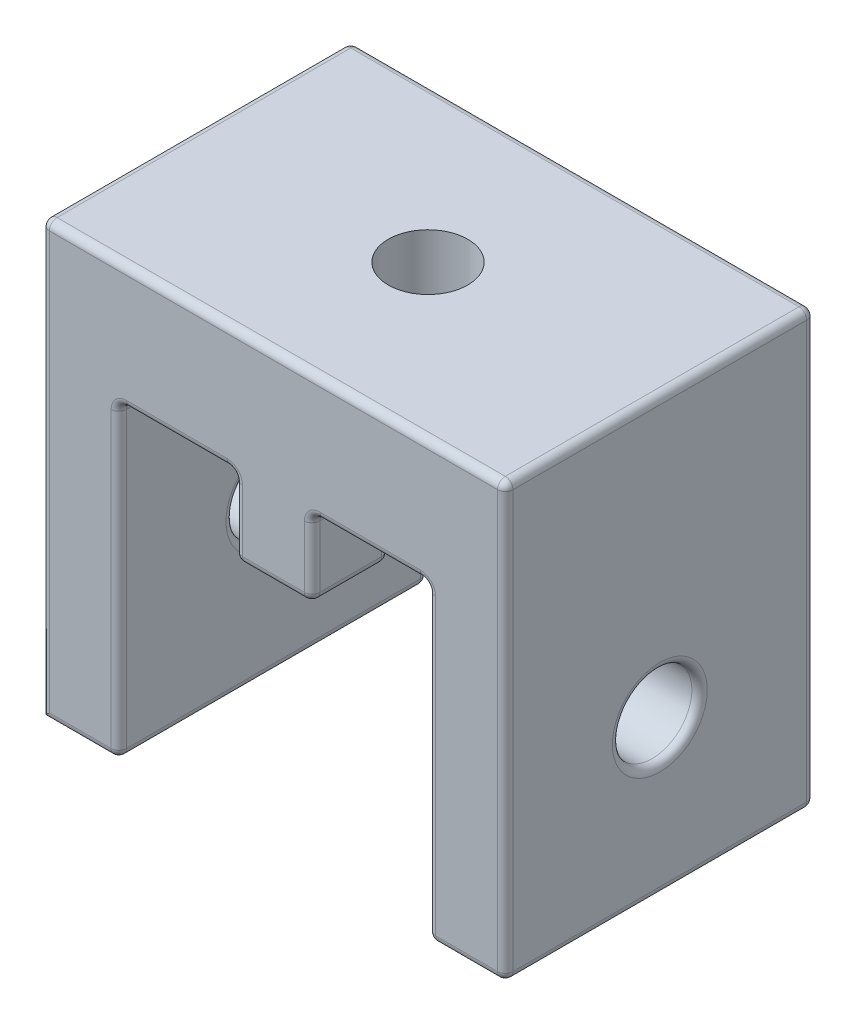
SolidWorks part; units mm, degrees
ref_plane "Front Plane" through (0, 0, 0) normal (0, 0, 1) x (1, 0, 0)
ref_plane "Top Plane" through (0, 0, 0) normal (0, 1, 0) x (1, 0, 0)
ref_plane "Right Plane" through (0, 0, 0) normal (1, 0, 0) x (0, 0, -1)
sketch "Sketch1" plane through (0, 0, 0) normal (0, 0, 1) x (1, 0, 0)
  line L0 (0, 0) -> (6.35, 0) construction
  line L1 (0, 0) -> (6.35, 0)
  line L2 (0, 0) -> (0, 35.56)
  line L3 (0, 35.56) -> (38.1, 35.56)
  line L4 (38.1, 0) -> (38.1, 35.56)
  line L5 (6.35, 0) -> (6.35, 25.4) construction
  line L6 (6.35, 25.4) -> (31.75, 25.4) construction
  line L7 (31.75, 25.4) -> (31.75, 0) construction
  line L8 (31.75, 0) -> (38.1, 0) construction
  line L9 (6.35, 0) -> (6.35, 25.4)
  line L10 (6.35, 25.4) -> (31.75, 25.4)
  line L11 (31.75, 25.4) -> (31.75, 0)
  line L12 (31.75, 0) -> (38.1, 0)
  dimension "D1" = 6.35
  dimension "D2" = 6.35
  dimension "D3" = 25.4
  dimension "D4" = 38.1
  dimension "D5" = 35.56
  dimension "D6" = 25.4
extrude "Boss-Extrude1" add sketch "Sketch1" along normal blind 25.4
sketch "Sketch2" plane through (0, 25.4, 0) normal (0, -1, 0) x (1, 0, 0)
  line L0 (0, 0) -> (19.05, 0) construction
  line L1 (6.35, 0) -> (31.75, 0) construction
  line L2 (19.05, 0) -> (19.05, 3.175) construction
  line L4 (22.225, 6.35) -> (15.875, 6.35)
  line L5 (22.225, 6.35) -> (22.225, 0)
  line L6 (22.225, 0) -> (15.875, 0)
  line L7 (15.875, 6.35) -> (15.875, 0)
  line L8 (22.225, 6.35) -> (15.875, 0) construction
  line L9 (22.225, 0) -> (15.875, 6.35) construction
  dimension "D1" = 6.35
  dimension "D2" = 6.35
extrude "Boss-Extrude2" add sketch "Sketch2" along normal blind 6.35
ref_plane "Plane1" through (0, 0, 12.7) normal (0, 0, 1) x (1, 0, 0)
mirror "Mirror1" about plane through (0, 0, 12.7) normal (0, 0, 1) of "Boss-Extrude2"
hole_wizard "#97 (0.0059) Diameter Hole3" positions "Sketch4" profile "Sketch3" hole size "#97" standard "Ansi Inch" end condition through all
sketch "Sketch4" plane through (0, 35.56, 0) normal (0, 1, 0) x (-1, 0, 0)
  line L0 (-38.1, 0) -> (0, 0) construction
  line L1 (0, 25.4) -> (0, 0) construction
  point P0 (-19.05, 12.7)
  point P2 (-19.05, 0)
  dimension "D1" = 12.7
  dimension "D2" = 19.05
sketch "Sketch3" plane through (19.05, 35.56, 12.7) normal (1, 0, 0) x (0, 0, 1)
  line L0 (0, 0) -> (0, 35.56)
  line L1 (0, 35.56) -> (3.2639, 35.56)
  line L2 (3.2639, 35.56) -> (3.2639, 0)
  line L5 (3.2639, 0) -> (0, 0)
  line L11 (0, -6.35) -> (0, 107.95) construction
  dimension "Thru Hole Dia." = 6.5278
  dimension "Thru Hole Depth" = 35.56
hole_wizard "#97 (0.0059) Diameter Hole1" positions "Sketch6" profile "Sketch5" hole size "#97" standard "Ansi Inch"
sketch "Sketch6" plane through (6.35, 0, 0) normal (1, 0, 0) x (0, 0, -1)
  line L0 (0, 0) -> (0, 25.4) construction
  line L1 (-25.4, 25.4) -> (0, 25.4) construction
  point P0 (-12.7, 12.7)
  dimension "D1" = 12.7
  dimension "D2" = 12.7
sketch "Sketch5" plane through (6.35, 12.7, 12.7) normal (0, 1, 0) x (0, 0, -1)
  line L0 (0, 0) -> (0, 6.35)
  line L1 (0, 6.35) -> (3.2639, 6.35)
  line L2 (3.2639, 6.35) -> (3.2639, 0)
  line L5 (3.2639, 0) -> (0, 0)
  line L11 (0, -6.35) -> (0, 107.95) construction
  dimension "Thru Hole Dia." = 6.5278
  dimension "Thru Hole Depth" = 6.35
hole_wizard "#97 (0.0059) Diameter Hole2" positions "Sketch8" profile "Sketch7" hole size "#97" standard "Ansi Inch" end condition through all
sketch "Sketch8" plane through (31.75, 0, 0) normal (-1, 0, 0) x (0, 0, 1)
  line L0 (25.4, 25.4) -> (0, 25.4) construction
  line L1 (0, 25.4) -> (0, 0) construction
  point P0 (12.7, 12.7)
  dimension "D1" = 12.7
  dimension "D2" = 12.7
sketch "Sketch7" plane through (31.75, 12.7, 12.7) normal (0, 1, 0) x (0, 0, 1)
  line L0 (0, 0) -> (0, 6.35)
  line L1 (0, 6.35) -> (3.2639, 6.35)
  line L2 (3.2639, 6.35) -> (3.2639, 0)
  line L5 (3.2639, 0) -> (0, 0)
  line L11 (0, -6.35) -> (0, 107.95) construction
  dimension "Thru Hole Dia." = 6.5278
  dimension "Thru Hole Depth" = 6.35
ref_plane "Plane2" through (0, 25.4, 0) normal (0, 1, 0) x (-1, 0, 0)
sketch "Sketch9" plane through (0, 25.4, 0) normal (0, 1, 0) x (-1, 0, 0)
  line L3 (-25.3558, 12.7) -> (-22.2029, 7.239)
  line L4 (-22.2029, 7.239) -> (-15.8971, 7.239)
  line L5 (-15.8971, 7.239) -> (-12.7442, 12.7)
  line L6 (-12.7442, 12.7) -> (-15.8971, 18.161)
  line L7 (-15.8971, 18.161) -> (-22.2029, 18.161)
  line L8 (-22.2029, 18.161) -> (-25.3558, 12.7)
extrude "Boss-Extrude3" add sketch "Sketch9" along normal blind 5.08 separate body
combine bodies "Combine1" operation type subtract main body 106 bodies to subtract 107
fillet "Fillet1" radius 0.635 51 edges at (19.05, 25.4, 6.35) (19.05, 25.4, 19.05) (38.1, 0, 12.7) (38.1, 35.56, 12.7) (15.875, 22.225, 6.35) (15.875, 25.4, 3.175) (3.175, 0, 0) (11.1125, 25.4, 0) (15.875, 22.225, 0) (26.9875, 25.4, 0) (34.925, 0, 0) (38.1, 17.78, 0) (19.05, 35.56, 0) (0, 17.78, 0) (22.225, 22.225, 0) (22.225, 22.225, 6.35) (22.225, 25.4, 3.175) (15.875, 22.225, 19.05) (15.875, 25.4, 22.225) (19.05, 35.56, 25.4) (38.1, 17.78, 25.4) (34.925, 0, 25.4) (26.9875, 25.4, 25.4) (15.875, 22.225, 25.4) (11.1125, 25.4, 25.4) (3.175, 0, 25.4) (0, 17.78, 25.4) (22.225, 22.225, 19.05) (22.225, 22.225, 25.4) (22.225, 25.4, 22.225) (19.05, 19.05, 6.35) (22.225, 19.05, 3.175) (19.05, 19.05, 0) (15.875, 19.05, 3.175) (19.05, 19.05, 19.05) (19.05, 19.05, 25.4) (22.225, 19.05, 22.225) (15.875, 19.05, 22.225) (6.35, 0, 12.7) (6.35, 12.7, 25.4) (6.35, 25.4, 12.7) (6.35, 12.7, 0) (6.35, 12.7, 9.4361) (31.75, 25.4, 12.7) (31.75, 12.7, 25.4) (31.75, 0, 12.7) (31.75, 12.7, 0) (31.75, 12.7, 15.9639) (0, 12.7, 9.4361) (0, 35.56, 12.7) (38.1, 12.7, 15.9639)
